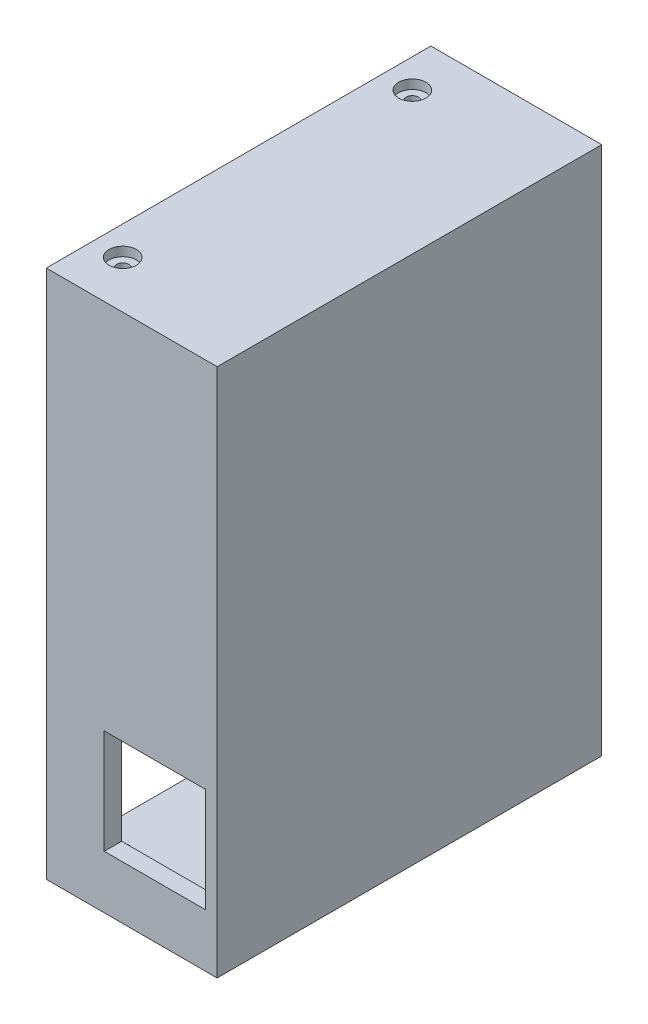
SolidWorks part; units mm, degrees
ref_plane "Front Plane" through (0, 0, 0) normal (1, 0, 0) x (0, 1, 0)
ref_plane "Top Plane" through (0, 0, 0) normal (0, 0, 1) x (0, 1, 0)
ref_plane "Right Plane" through (0, 0, 0) normal (0, 1, 0) x (-1, 0, 0)
sketch "Sketch1" plane through (0, 0, 0) normal (1, 0, 0) x (0, 1, 0)
  line L0 (58.035, 42.16) -> (-58.035, 42.16)
  line L1 (53.975, -38.1) -> (-53.975, -38.1) construction
  line L2 (53.975, -38.1) -> (53.975, 38.1) construction
  line L3 (53.975, 38.1) -> (-53.975, 38.1) construction
  line L4 (-53.975, -38.1) -> (-53.975, 38.1) construction
  line L5 (-58.035, -42.16) -> (-58.035, 42.16)
  line L6 (58.035, -42.16) -> (-58.035, -42.16)
  line L7 (58.035, -42.16) -> (58.035, 42.16)
  dimension "D1" = 4.06
extrude "Boss-Extrude1" add sketch "Sketch1" along normal blind 2.54
sketch "Sketch2" plane through (0, 0, 0) normal (-1, 0, 0) x (0, -1, 0)
  line L0 (54.225, -38.35) -> (54.225, 38.35)
  line L1 (58.035, -42.16) -> (-58.035, -42.16)
  line L2 (58.035, -42.16) -> (58.035, 42.16)
  line L3 (58.035, 42.16) -> (-58.035, 42.16)
  line L4 (-58.035, -42.16) -> (-58.035, 42.16)
  line L5 (54.225, 38.35) -> (-54.225, 38.35)
  line L6 (-54.225, -38.35) -> (-54.225, 38.35)
  line L7 (54.225, -38.35) -> (-54.225, -38.35)
  dimension "D1" = 3.81
extrude "Boss-Extrude2" add sketch "Sketch2" along normal up to surface (34.925 mm away)
sketch "Sketch4" plane through (0, -53.975, 0) normal (0, -1, 0) x (1, 0, 0)
  circle A0 centre (-28.575, 31.75) radius 1.35
  circle A1 centre (-28.575, -31.75) radius 1.35
  dimension "D1" = 2.7
  dimension "D2" = 2.7
extrude "Cut-Extrude1" cut sketch "Sketch4" along normal up to vertex
sketch "Sketch5" plane through (0, 53.975, 0) normal (0, 1, 0) x (-1, 0, 0)
  circle A0 centre (28.575, -31.75) radius 1.35
  circle A1 centre (28.575, 31.75) radius 1.35
  dimension "D1" = 2.7
  dimension "D2" = 2.7
extrude "Cut-Extrude2" cut sketch "Sketch5" along normal up to vertex
sketch "Sketch6" plane through (0, -58.035, 0) normal (0, -1, 0) x (1, 0, 0)
  circle A0 centre (-28.575, 31.75) radius 3
  circle A1 centre (-28.575, -31.75) radius 3
  dimension "D1" = 6
  dimension "D2" = 6
sketch "Sketch7" plane through (0, 58.035, 0) normal (0, 1, 0) x (-1, 0, 0)
  circle A0 centre (28.575, -31.75) radius 3
  circle A1 centre (28.575, 31.75) radius 3
  dimension "D1" = 6
  dimension "D2" = 6
extrude "Cut-Extrude3" cut sketch "Sketch7" against normal blind 2
extrude "Cut-Extrude4" cut sketch "Sketch6" against normal blind 2
sketch "Sketch8" plane through (0, -53.975, 0) normal (0, -1, 0) x (1, 0, 0)
  line L1 (0, 0) -> (-22.225, 0)
  line L2 (0, 0) -> (0, -25.4)
  line L3 (0, -25.4) -> (-22.225, -25.4)
  line L4 (-22.225, 0) -> (-22.225, -25.4)
sketch "Sketch10" plane through (0, 0, 38.1) normal (0, 0, 1) x (1, 0, 0)
  line L1 (0, -23.495) -> (-22.225, -23.495)
  line L2 (0, -23.495) -> (0, -46.355)
  line L3 (0, -46.355) -> (-22.225, -46.355)
  line L4 (-22.225, -23.495) -> (-22.225, -46.355)
sketch "Sketch11" plane through (0, 0, -38.1) normal (0, 0, -1) x (1, 0, 0)
  line L1 (0, 46.355) -> (-22.225, 46.355)
  line L2 (0, 46.355) -> (0, 23.495)
  line L3 (0, 23.495) -> (-22.225, 23.495)
  line L4 (-22.225, 46.355) -> (-22.225, 23.495)
extrude "Cut-Extrude5" cut sketch "Sketch11" along normal up to vertex
extrude "Cut-Extrude6" cut sketch "Sketch8" along normal up to vertex
extrude "Cut-Extrude7" cut sketch "Sketch10" along normal up to vertex
equation "\"CASE_CLEARANCE\"= 0.25mm"
equation "\"TOP_WALL_WIDTH\"= 0.15in"
equation "\"SCREW_HEAD_DIAM\"= 6mm"
equation "\"SCREW_HEAD_DEPTH\"= 2mm"
equation "\"D1@Sketch1\"=\"CASE_CLEARANCE\"+\"TOP_WALL_WIDTH\""
equation "\"D1@Sketch2\"=\"TOP_WALL_WIDTH\""
equation "\"M2.5_HOLE\"= 2.7mm"
equation "\"D1@Sketch4\"=\"M2.5_HOLE\""
equation "\"D2@Sketch4\"=\"M2.5_HOLE\""
equation "\"D1@Sketch5\"=\"M2.5_HOLE\""
equation "\"D2@Sketch5\"=\"M2.5_HOLE\""
equation "\"D1@Sketch6\"=\"SCREW_HEAD_DIAM\""
equation "\"D2@Sketch6\"=\"SCREW_HEAD_DIAM\""
equation "\"D1@Sketch7\"=\"SCREW_HEAD_DIAM\""
equation "\"D2@Sketch7\"=\"SCREW_HEAD_DIAM\""
equation "\"D1@Cut-Extrude3\"=\"SCREW_HEAD_DEPTH\""
equation "\"D1@Cut-Extrude4\"=\"SCREW_HEAD_DEPTH\""
